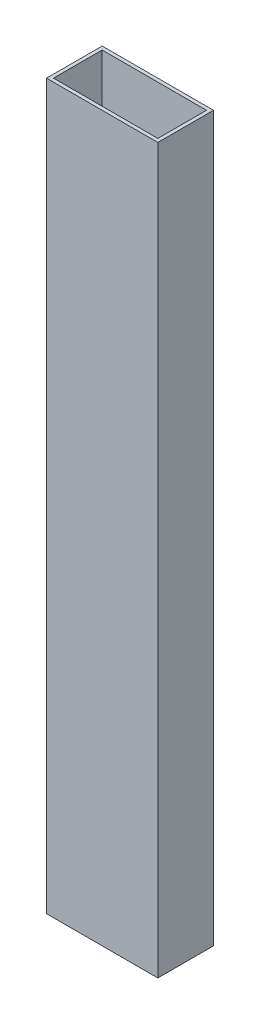
SolidWorks part; units mm, degrees
ref_plane "Front Plane" through (0, 0, 0) normal (0, 0, 1) x (1, 0, 0)
ref_plane "Top Plane" through (0, 0, 0) normal (0, 1, 0) x (1, 0, 0)
ref_plane "Right Plane" through (0, 0, 0) normal (1, 0, 0) x (0, 0, -1)
sketch "Sketch1" plane through (0, 0, 0) normal (0, 1, 0) x (1, 0, 0)
  line L1 (0, 0) -> (50.8, 0)
  line L2 (0, 0) -> (0, 25.4)
  line L3 (0, 25.4) -> (50.8, 25.4)
  line L4 (50.8, 0) -> (50.8, 25.4)
  dimension "D1" = 50.8
  dimension "D2" = 25.4
extrude "Extrude-Thin1" add sketch "Sketch1" along normal blind 330.2 thin thin type one direction reverse wall 1.5875
